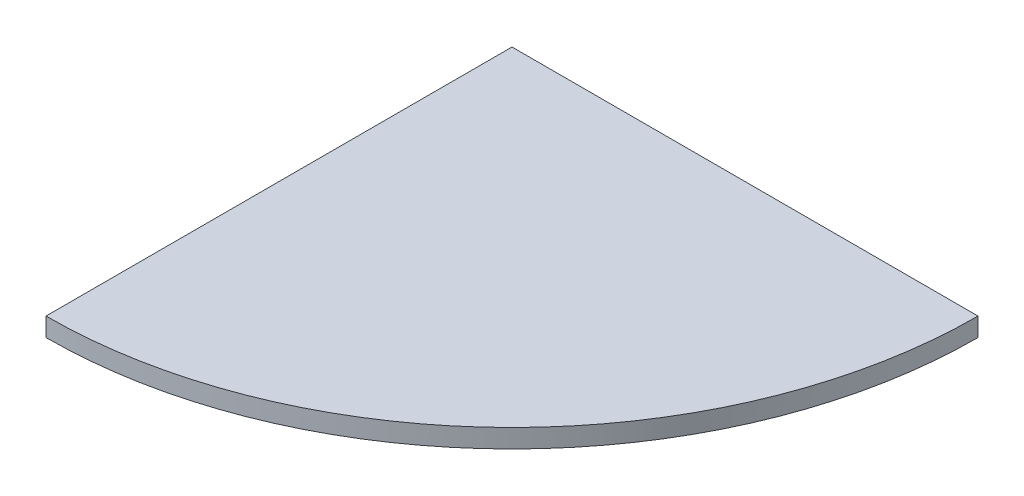
SolidWorks part; units mm, degrees
ref_plane "Front Plane" through (0, 0, 0) normal (0, 0, 1) x (1, 0, 0)
ref_plane "Top Plane" through (0, 0, 0) normal (0, 1, 0) x (1, 0, 0)
ref_plane "Right Plane" through (0, 0, 0) normal (1, 0, 0) x (0, 0, -1)
sketch "Sketch1" plane through (0, 0, 0) normal (0, 1, 0) x (1, 0, 0)
  line L1 (0, 0) -> (450, 0)
  line L2 (0, -450) -> (0, 0)
  arc A0 (450, 0) -> (0, -450) centre (0, 0) cw
  dimension "D1" = 450
extrude "Boss-Extrude1" add sketch "Sketch1" along normal blind 18
